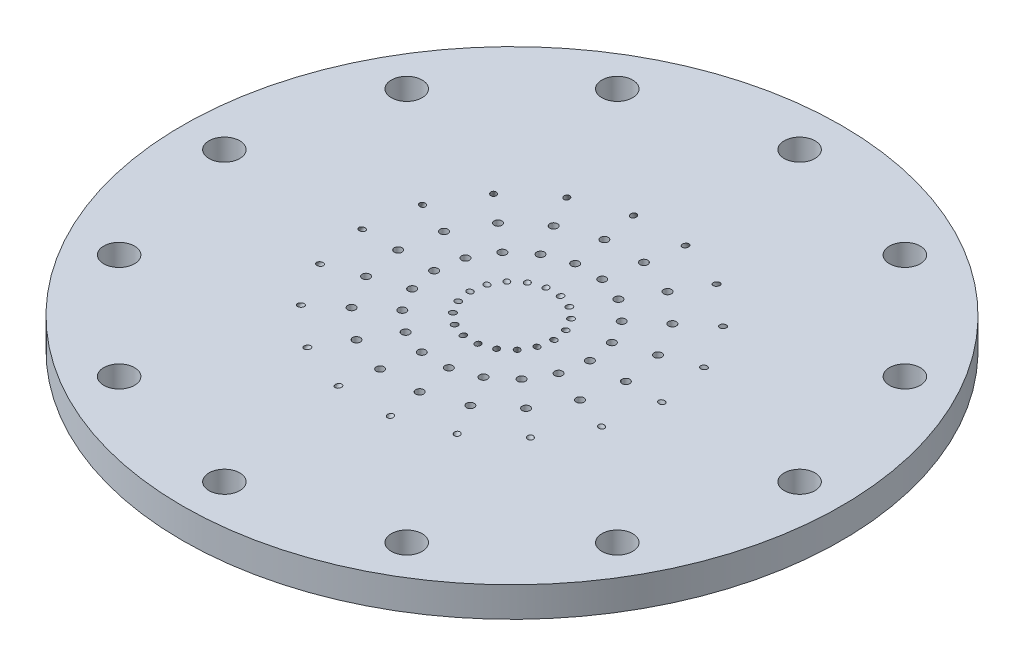
SolidWorks part; units mm, degrees
material "6061-T6 (SS)"
ref_plane "Front Plane" through (0, 0, 0) normal (0, 0, 1) x (1, 0, 0)
ref_plane "Top Plane" through (0, 0, 0) normal (0, 1, 0) x (1, 0, 0)
ref_plane "Right Plane" through (0, 0, 0) normal (1, 0, 0) x (0, 0, -1)
sketch "Sketch1" plane through (0, 0, 0) normal (0, 1, 0) x (1, 0, 0)
  circle A0 centre (0, 0) radius 69.85
  dimension "D1" = 139.7
extrude "Boss-Extrude1" add sketch "Sketch1" along normal blind 6.35 contours A0
sketch "Sketch2" plane through (0, 6.35, 0) normal (0, 1, 0) x (1, 0, 0)
  circle A0 centre (0, 0) radius 8.89
  circle A1 centre (0, 0) radius 16.51
  circle A2 centre (0, 0) radius 24.13
  circle A3 centre (0, 0) radius 31.75
  dimension "D1" = 17.78
  dimension "D2" = 33.02
  dimension "D3" = 48.26
  dimension "D4" = 63.5
sketch "Sketch3" plane through (0, 0, 0) normal (0, 0, 1) x (1, 0, 0)
  line L0 (8.89, 6.35) -> (0, -9.0479)
  line L1 (8.89, 6.35) -> (-8.89, 6.35) construction
  line L2 (16.51, 6.35) -> (-16.51, 6.35) construction
  line L3 (0, 0) -> (0, -9.0479) construction
  line L4 (0, -9.0479) -> (-8.5376, -4.1187) construction
  dimension "D1" = 30
ref_plane "Plane1" through (-3.9179, -6.7859, 0) normal (0.5, 0.866, 0) x (-0.866, 0.5, 0)
sketch "Sketch4" plane through (-3.9179, -6.7859, 0) normal (0.5, 0.866, 0) x (-0.866, 0.5, 0)
  line L0 (-4.524, 0) -> (5.3344, 0) construction
  circle A0 centre (-4.524, 0) radius 0.5906
  dimension "D1" = 1.1811
extrude "Cut-Extrude1" cut sketch "Sketch4" along normal through all
sketch "Sketch5" plane through (0, 0, 0) normal (0, 0, 1) x (1, 0, 0)
  line L0 (31.75, 6.35) -> (35.4162, 0)
  line L3 (31.75, 6.35) -> (-31.75, 6.35) construction
  line L4 (35.4162, 0) -> (0, 0) construction
  line L5 (31.75, 6.35) -> (52.6029, 18.3894) construction
  dimension "D1" = 60
ref_plane "Plane2" through (5.1879, -8.9857, 0) normal (0.5, -0.866, 0) x (0.866, 0.5, 0)
sketch "Sketch6" plane through (5.1879, -8.9857, 0) normal (0.5, -0.866, 0) x (0.866, 0.5, 0)
  circle A0 centre (30.6713, 0) radius 0.5906
  dimension "D1" = 1.1811
extrude "Cut-Extrude2" cut sketch "Sketch6" against normal through all both and the other way through all
sketch "Sketch7" plane through (0, 6.35, 0) normal (0, 1, 0) x (1, 0, 0)
  line L0 (0, 0) -> (31.75, 0) construction
  circle A0 centre (0, 0) radius 31.75 construction
  circle A1 centre (24.13, 0) radius 0.8255
  circle A2 centre (0, 0) radius 24.13 construction
  circle A3 centre (16.51, 0) radius 0.8255
  circle A7 centre (0, 0) radius 16.51 construction
  dimension "D1" = 1.651
extrude "LOx Holes" cut sketch "Sketch7" against normal through all both and the other way through all
pattern_circular "CirPattern1" count 18 over 360 about axis through (0, 0, 0) along (0, 1, 0) of "Cut-Extrude1", "Cut-Extrude2", "LOx Holes"
sketch "Sketch8" plane through (0, 0, 0) normal (0, -1, 0) x (1, 0, 0)
  circle A0 centre (0, 0) radius 60.96 construction
  circle A1 centre (-60.96, 0) radius 3.2639
  point P5 (0, 0)
  dimension "D1" = 121.92
  dimension "D2" = 6.5278
extrude "Cut-Extrude4" cut sketch "Sketch8" against normal through all
pattern_circular "CirPattern2" count 12 over 360 about axis through (0, 0, 0) along (0, 1, 0) of "Cut-Extrude4"
